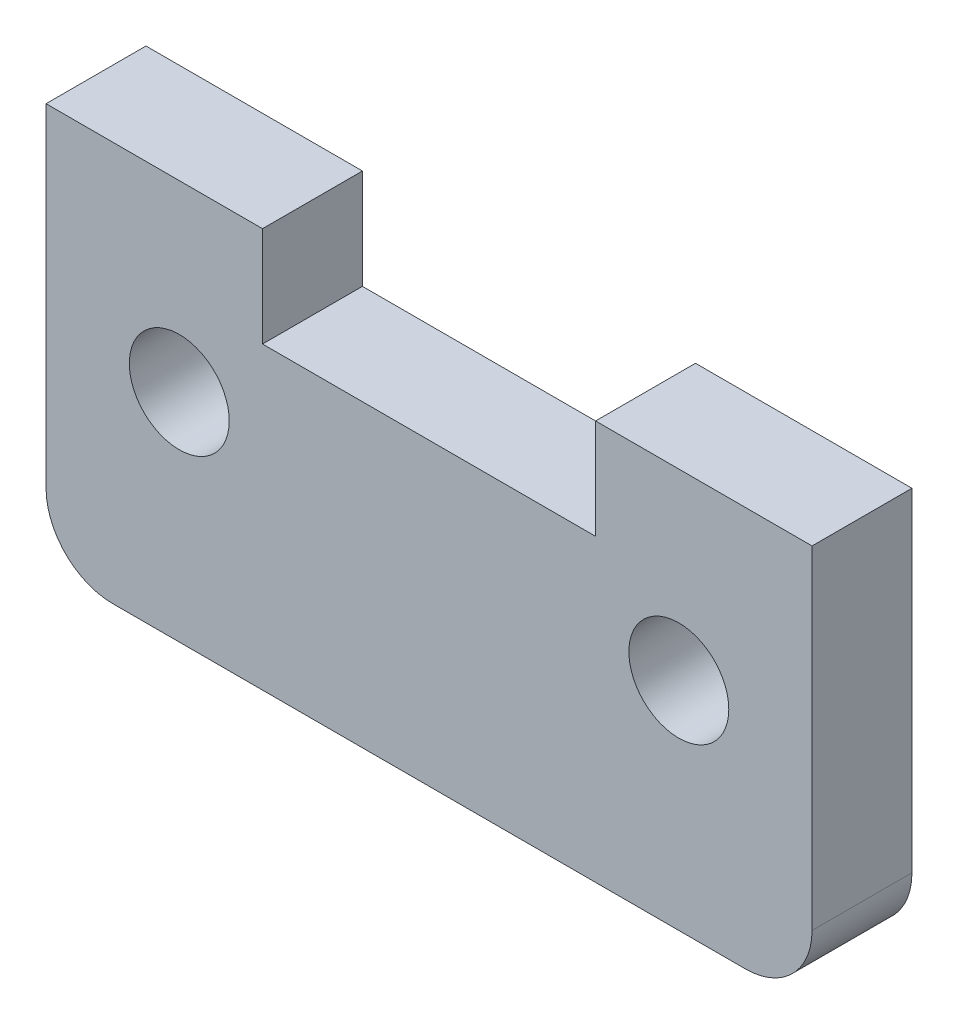
SolidWorks part; units mm, degrees
ref_plane "Front Plane" through (0, 0, 0) normal (0, 0, 1) x (1, 0, 0)
ref_plane "Top Plane" through (0, 0, 0) normal (0, 1, 0) x (1, 0, 0)
ref_plane "Right Plane" through (0, 0, 0) normal (1, 0, 0) x (0, 0, -1)
sketch "Sketch1" plane through (0, 0, 0) normal (0, 0, 1) x (1, 0, 0)
  line L0 (-10.3229, 5.5881) -> (-10.3229, 2.5881)
  line L1 (-16.8229, 5.5881) -> (-10.3229, 5.5881)
  line L2 (-16.8229, 5.5881) -> (-16.8229, -4.4119)
  line L3 (-14.8229, -6.4119) -> (4.1771, -6.4119)
  line L4 (6.1771, 5.5881) -> (6.1771, -4.4119)
  line L5 (-10.3229, 2.5881) -> (-0.3229, 2.5881)
  line L6 (-0.3229, 2.5881) -> (-0.3229, 5.5881)
  line L7 (-0.3229, 5.5881) -> (6.1771, 5.5881)
  circle A0 centre (-12.8229, 0.0881) radius 1.5
  circle A1 centre (2.1771, 0.0881) radius 1.5
  arc A2 (4.1771, -6.4119) -> (6.1771, -4.4119) centre (4.1771, -4.4119) ccw
  arc A3 (-16.8229, -4.4119) -> (-14.8229, -6.4119) centre (-14.8229, -4.4119) ccw
  point P16 (-16.8229, -6.4119)
  dimension "D1" = 3
  dimension "D2" = 3
  dimension "D10" = 2
  dimension "D3" = 15
  dimension "D4" = 4
  dimension "D5" = 23
  dimension "D6" = 6.5
  dimension "D7" = 12
  dimension "D8" = 10
  dimension "D9" = 3
extrude "Boss-Extrude1" add sketch "Sketch1" along normal blind 3
